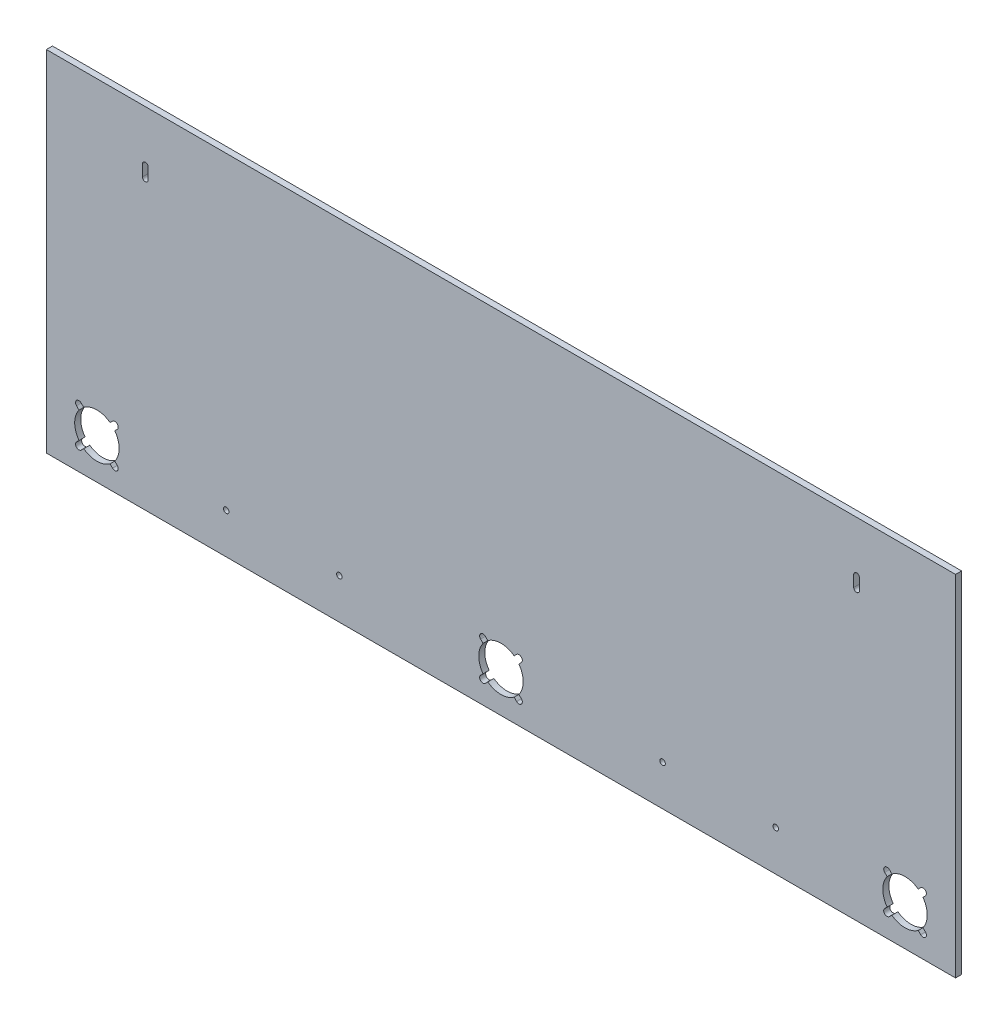
SolidWorks part; units mm, degrees
ref_plane "Front Plane" through (0, 0, 0) normal (0, 0, 1) x (1, 0, 0)
ref_plane "Top Plane" through (0, 0, 0) normal (0, 1, 0) x (1, 0, 0)
ref_plane "Right Plane" through (0, 0, 0) normal (1, 0, 0) x (0, 0, -1)
sketch "Sketch1" plane through (0, 0, 0) normal (0, 0, 1) x (1, 0, 0)
  line L1 (-357.1875, -137.3187) -> (357.1875, -137.3187)
  line L2 (-357.1875, -137.3187) -> (-357.1875, 137.3188)
  line L3 (-357.1875, 137.3188) -> (357.1875, 137.3188)
  line L4 (357.1875, -137.3187) -> (357.1875, 137.3188)
  line L5 (-357.1875, -137.3187) -> (357.1875, 137.3188) construction
  line L6 (-357.1875, 137.3188) -> (357.1875, -137.3187) construction
  point P0 (0, 0)
  dimension "D1" = 714.375
  dimension "D2" = 274.6375
extrude "Boss-Extrude1" add sketch "Sketch1" along normal blind 4.7625
sketch "Sketch2" plane through (0, 0, 4.7625) normal (0, 0, 1) x (1, 0, 0)
  line L0 (-357.1875, -137.3187) -> (-357.1875, -73.8187) construction
  line L1 (-357.1875, 137.3188) -> (-357.1875, -137.3187) construction
  line L2 (-357.1875, -105.5687) -> (357.1875, -105.5687) construction
  line L3 (12.286, -89.5705) -> (10.3514, -91.5051)
  line L4 (0, -105.5687) -> (0, -137.3187) construction
  line L5 (-357.1875, -137.3187) -> (357.1875, -137.3187) construction
  line L6 (357.1875, -137.3187) -> (357.1875, 137.3188) construction
  line L7 (0, -105.5687) -> (14.1421, -91.4266) construction
  line L8 (14.1421, -91.4266) -> (12.286, -89.5705) construction
  line L9 (12.286, -89.5705) -> (15.9983, -93.2828) construction
  line L10 (15.9983, -93.2828) -> (14.0637, -95.2174)
  line L11 (15.9983, -117.8547) -> (14.0637, -115.9201)
  line L12 (12.286, -121.567) -> (10.3514, -119.6324)
  line L13 (0, -105.5687) -> (14.1421, -119.7109) construction
  line L14 (14.1421, -119.7109) -> (15.9983, -117.8547) construction
  line L15 (15.9983, -117.8547) -> (12.286, -121.567) construction
  line L16 (-12.286, -121.567) -> (-10.3514, -119.6324)
  line L17 (-15.9983, -117.8547) -> (-14.0637, -115.9201)
  line L18 (0, -105.5687) -> (-14.1421, -119.7109) construction
  line L19 (-14.1421, -119.7109) -> (-12.286, -121.567) construction
  line L20 (-12.286, -121.567) -> (-15.9983, -117.8547) construction
  line L21 (-15.9983, -93.2828) -> (-14.0637, -95.2174)
  line L22 (-12.286, -89.5705) -> (-10.3514, -91.5051)
  line L23 (0, -105.5687) -> (-14.1421, -91.4266) construction
  line L24 (-14.1421, -91.4266) -> (-15.9983, -93.2828) construction
  line L25 (-15.9983, -93.2828) -> (-12.286, -89.5705) construction
  line L26 (0, -105.5687) -> (-317.5, -105.5687) construction
  line L27 (0, -105.5687) -> (317.5, -105.5687) construction
  line L28 (-317.5, -105.5687) -> (0, -105.5687) construction
  line L29 (-158.75, -105.5687) -> (-158.75, 137.3188) construction
  line L30 (357.1875, 137.3188) -> (-357.1875, 137.3188) construction
  line L31 (317.5, -105.5687) -> (0, -105.5687) construction
  line L32 (158.75, -105.5687) -> (158.75, 137.3188) construction
  line L33 (-301.5017, -93.2828) -> (-305.214, -89.5705) construction
  line L34 (-303.3579, -91.4266) -> (-301.5017, -93.2828) construction
  line L35 (-317.5, -105.5687) -> (-303.3579, -91.4266) construction
  line L36 (-305.214, -121.567) -> (-301.5017, -117.8547) construction
  line L37 (-303.3579, -119.7109) -> (-305.214, -121.567) construction
  line L38 (-317.5, -105.5687) -> (-303.3579, -119.7109) construction
  line L39 (-333.4983, -117.8547) -> (-329.786, -121.567) construction
  line L40 (-331.6421, -119.7109) -> (-333.4983, -117.8547) construction
  line L41 (-317.5, -105.5687) -> (-331.6421, -119.7109) construction
  line L42 (-329.786, -89.5705) -> (-333.4983, -93.2828) construction
  line L43 (-331.6421, -91.4266) -> (-329.786, -89.5705) construction
  line L44 (-317.5, -105.5687) -> (-331.6421, -91.4266) construction
  line L45 (-317.5, -105.5687) -> (-317.5, -137.3187) construction
  line L46 (-305.214, -89.5705) -> (-307.1486, -91.5051)
  line L47 (-301.5017, -93.2828) -> (-303.4363, -95.2174)
  line L48 (-301.5017, -117.8547) -> (-303.4363, -115.9201)
  line L49 (-305.214, -121.567) -> (-307.1486, -119.6324)
  line L50 (-329.786, -121.567) -> (-327.8514, -119.6324)
  line L51 (-333.4983, -117.8547) -> (-331.5637, -115.9201)
  line L52 (-333.4983, -93.2828) -> (-331.5637, -95.2174)
  line L53 (-329.786, -89.5705) -> (-327.8514, -91.5051)
  line L54 (333.4983, -93.2828) -> (329.786, -89.5705) construction
  line L55 (331.6421, -91.4266) -> (333.4983, -93.2828) construction
  line L56 (317.5, -105.5687) -> (331.6421, -91.4266) construction
  line L57 (329.786, -121.567) -> (333.4983, -117.8547) construction
  line L58 (331.6421, -119.7109) -> (329.786, -121.567) construction
  line L59 (317.5, -105.5687) -> (331.6421, -119.7109) construction
  line L60 (301.5017, -117.8547) -> (305.214, -121.567) construction
  line L61 (303.3579, -119.7109) -> (301.5017, -117.8547) construction
  line L62 (317.5, -105.5687) -> (303.3579, -119.7109) construction
  line L63 (305.214, -89.5705) -> (301.5017, -93.2828) construction
  line L64 (303.3579, -91.4266) -> (305.214, -89.5705) construction
  line L65 (317.5, -105.5687) -> (303.3579, -91.4266) construction
  line L66 (317.5, -105.5687) -> (317.5, -137.3187) construction
  line L67 (329.786, -89.5705) -> (327.8514, -91.5051)
  line L68 (333.4983, -93.2828) -> (331.5637, -95.2174)
  line L69 (333.4983, -117.8547) -> (331.5637, -115.9201)
  line L70 (329.786, -121.567) -> (327.8514, -119.6324)
  line L71 (305.214, -121.567) -> (307.1486, -119.6324)
  line L72 (301.5017, -117.8547) -> (303.4363, -115.9201)
  line L73 (301.5017, -93.2828) -> (303.4363, -95.2174)
  line L74 (305.214, -89.5705) -> (307.1486, -91.5051)
  arc A0 (-14.0637, -95.2174) -> (-14.0637, -115.9201) centre (0, -105.5687) ccw
  arc A1 (15.9983, -93.2828) -> (12.286, -89.5705) centre (14.1421, -91.4266) ccw
  arc A2 (12.286, -121.567) -> (15.9983, -117.8547) centre (14.1421, -119.7109) ccw
  arc A3 (-15.9983, -117.8547) -> (-12.286, -121.567) centre (-14.1421, -119.7109) ccw
  arc A4 (-12.286, -89.5705) -> (-15.9983, -93.2828) centre (-14.1421, -91.4266) ccw
  arc A5 (10.3514, -91.5051) -> (-10.3514, -91.5051) centre (0, -105.5687) ccw
  arc A6 (14.0637, -115.9201) -> (14.0637, -95.2174) centre (0, -105.5687) ccw
  arc A7 (-10.3514, -119.6324) -> (10.3514, -119.6324) centre (0, -105.5687) ccw
  arc A8 (-307.1486, -119.6324) -> (-327.8514, -119.6324) centre (-317.5, -105.5687) cw
  arc A9 (-331.5637, -115.9201) -> (-331.5637, -95.2174) centre (-317.5, -105.5687) cw
  arc A10 (-327.8514, -91.5051) -> (-307.1486, -91.5051) centre (-317.5, -105.5687) cw
  arc A11 (-305.214, -89.5705) -> (-301.5017, -93.2828) centre (-303.3579, -91.4266) cw
  arc A12 (-301.5017, -117.8547) -> (-305.214, -121.567) centre (-303.3579, -119.7109) cw
  arc A13 (-329.786, -121.567) -> (-333.4983, -117.8547) centre (-331.6421, -119.7109) cw
  arc A14 (-333.4983, -93.2828) -> (-329.786, -89.5705) centre (-331.6421, -91.4266) cw
  arc A15 (-303.4363, -95.2174) -> (-303.4363, -115.9201) centre (-317.5, -105.5687) cw
  arc A16 (327.8514, -119.6324) -> (307.1486, -119.6324) centre (317.5, -105.5687) cw
  arc A17 (303.4363, -115.9201) -> (303.4363, -95.2174) centre (317.5, -105.5687) cw
  arc A18 (307.1486, -91.5051) -> (327.8514, -91.5051) centre (317.5, -105.5687) cw
  arc A19 (329.786, -89.5705) -> (333.4983, -93.2828) centre (331.6421, -91.4266) cw
  arc A20 (333.4983, -117.8547) -> (329.786, -121.567) centre (331.6421, -119.7109) cw
  arc A21 (305.214, -121.567) -> (301.5017, -117.8547) centre (303.3579, -119.7109) cw
  arc A22 (301.5017, -93.2828) -> (305.214, -89.5705) centre (303.3579, -91.4266) cw
  arc A23 (331.5637, -95.2174) -> (331.5637, -115.9201) centre (317.5, -105.5687) cw
  point P37 (0, -105.5688)
  dimension "D2" = 34.925
  dimension "D3" = 5.25
  dimension "D1" = 63.5
  dimension "D4" = 20
  dimension "D5" = 45
  dimension "D7" = 317.5
  dimension "D8" = 317.5
  dimension "D6" = 4
extrude "Cut-Extrude1" cut sketch "Sketch2" against normal through all
sketch "Sketch4" plane through (0, 0, 4.7625) normal (0, 0, 1) x (1, 0, 0)
  line L0 (0, 0) -> (0, 137.3188) construction
  line L1 (357.1875, 137.3188) -> (-357.1875, 137.3188) construction
  line L2 (-357.1875, 130.9688) -> (357.1875, 130.9688) construction
  line L3 (-357.1875, 137.3188) -> (-357.1875, -137.3187) construction
  line L4 (357.1875, -137.3187) -> (357.1875, 137.3188) construction
  line L5 (-357.1875, 130.9688) -> (0, 130.9688) construction
  line L6 (0, 130.9688) -> (357.1875, 130.9688) construction
  line L7 (-357.1875, 130.9688) -> (0, 130.9688) construction
  line L8 (0, 130.9688) -> (357.1875, 130.9688) construction
  line L9 (-279.4, 88.4238) -> (-279.4, 97.3138) construction
  line L10 (0, 67.4688) -> (357.1875, 67.4688) construction
  line L11 (357.1875, 67.4688) -> (-357.1875, 67.4687) construction
  line L12 (279.4, 86.8616) -> (279.4, 98.8759) construction
  line L13 (279.4, 88.4238) -> (279.4, 97.3138) construction
  line L14 (277.1521, 88.4238) -> (277.1521, 97.3138)
  line L15 (281.6479, 88.4238) -> (281.6479, 97.3138)
  line L16 (-277.1521, 88.4238) -> (-277.1521, 97.3138)
  line L17 (-281.6479, 88.4238) -> (-281.6479, 97.3138)
  line L18 (-279.4, 92.8688) -> (-279.4, 67.4688) construction
  line L19 (279.4, 92.8688) -> (279.4, 67.4688) construction
  line L20 (-279.4, 86.8616) -> (-279.4, 98.8759) construction
  arc A0 (277.1521, 88.4238) -> (281.6479, 88.4238) centre (279.4, 88.4238) ccw
  arc A1 (281.6479, 97.3138) -> (277.1521, 97.3138) centre (279.4, 97.3138) ccw
  arc A2 (-277.1521, 88.4238) -> (-281.6479, 88.4238) centre (-279.4, 88.4238) cw
  arc A3 (-281.6479, 97.3138) -> (-277.1521, 97.3138) centre (-279.4, 97.3138) cw
  point P21 (279.4, 92.8688)
  point P26 (-279.4, 92.8688)
  dimension "D1" = 6.35
  dimension "D2" = 63.5
  dimension "D3" = 8.89
  dimension "D4" = 4.4958
  dimension "D6" = 279.4
  dimension "D7" = 25.4
extrude "Cut-Extrude3" cut sketch "Sketch4" against normal through all
sketch "Sketch5" plane through (0, 0, 4.7625) normal (0, 0, 1) x (1, 0, 0)
  line L0 (0, 137.3188) -> (0, -137.3187) construction
  line L1 (357.1875, 137.3188) -> (-357.1875, 137.3188) construction
  line L2 (-357.1875, -137.3187) -> (357.1875, -137.3187) construction
  line L3 (-357.1875, -73.8187) -> (357.1875, -73.8187) construction
  line L4 (-357.1875, 137.3188) -> (-357.1875, -137.3187) construction
  line L5 (357.1875, -137.3187) -> (357.1875, 137.3188) construction
  line L6 (-357.1875, -73.8187) -> (-357.1875, -137.3187) construction
  line L7 (-357.1875, -105.5687) -> (357.1875, -105.5687) construction
  line L8 (0, -137.3187) -> (0, -105.5687) construction
  circle A0 centre (-127, -105.5687) radius 2.1527
  circle A1 centre (-215.9, -105.5687) radius 2.1527
  circle A2 centre (215.9, -105.5687) radius 2.1527
  circle A3 centre (127, -105.5687) radius 2.1527
  dimension "D2" = 4.3053
  dimension "D1" = 63.5
  dimension "D3" = 127
  dimension "D4" = 215.9
extrude "Cut-Extrude4" cut sketch "Sketch5" against normal up to next
